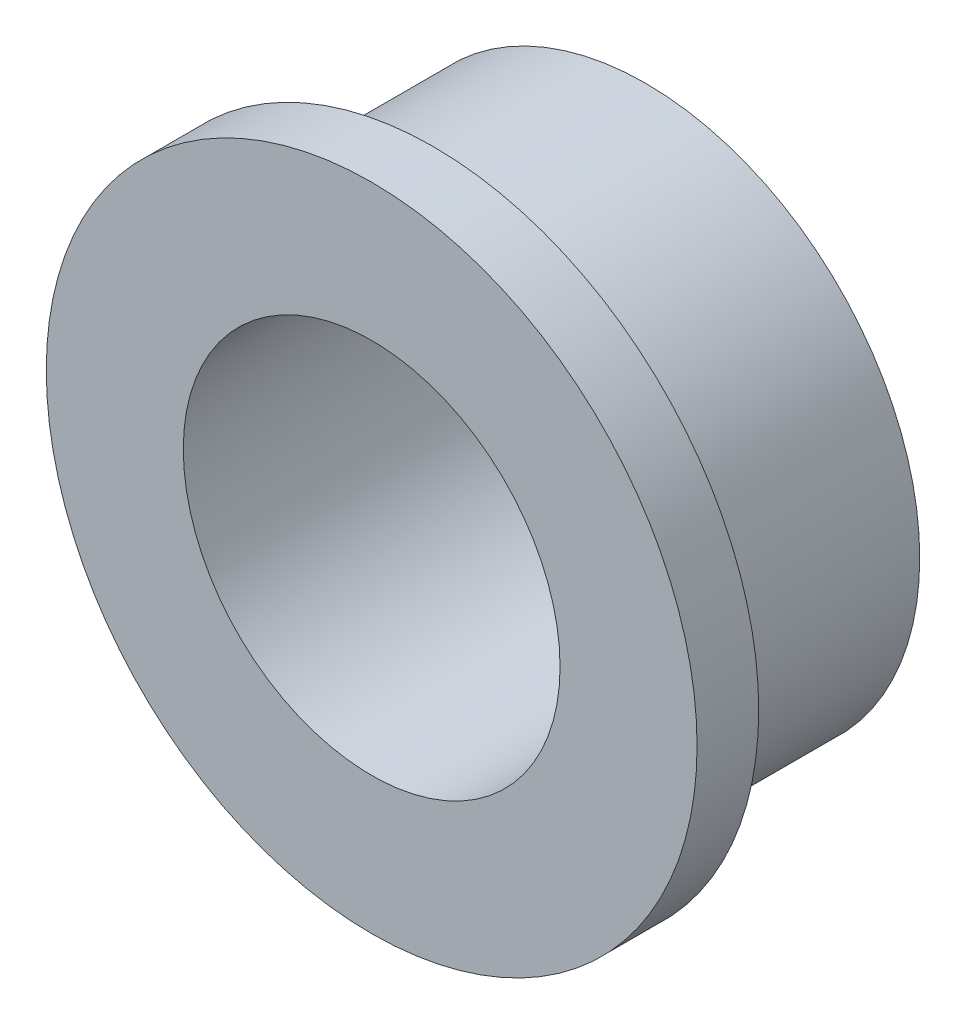
SolidWorks part; units mm, degrees
ref_plane "前视基准面" through (0, 0, 0) normal (0, 0, 1) x (1, 0, 0)
ref_plane "上视基准面" through (0, 0, 0) normal (0, 1, 0) x (1, 0, 0)
ref_plane "右视基准面" through (0, 0, 0) normal (1, 0, 0) x (0, 0, -1)
sketch "草图1" plane through (0, 0, 0) normal (0, 0, 1) x (1, 0, 0)
  circle A0 centre (0, 0) radius 4
  dimension "D1" = 8
extrude "凸台-拉伸1" add sketch "草图1" along normal blind 3.1
sketch "草图2" plane through (0, 0, 3.1) normal (0, 0, 1) x (1, 0, 0)
  circle A0 centre (0, 0) radius 4.75
  dimension "D1" = 9.5
extrude "凸台-拉伸2" add sketch "草图2" along normal blind 0.9
sketch "草图3" plane through (0, 0, 0) normal (0, 0, -1) x (-1, 0, 0)
  circle A0 centre (0, 0) radius 2.75
  dimension "D1" = 5.5
extrude "切除-拉伸1" cut sketch "草图3" against normal through all
